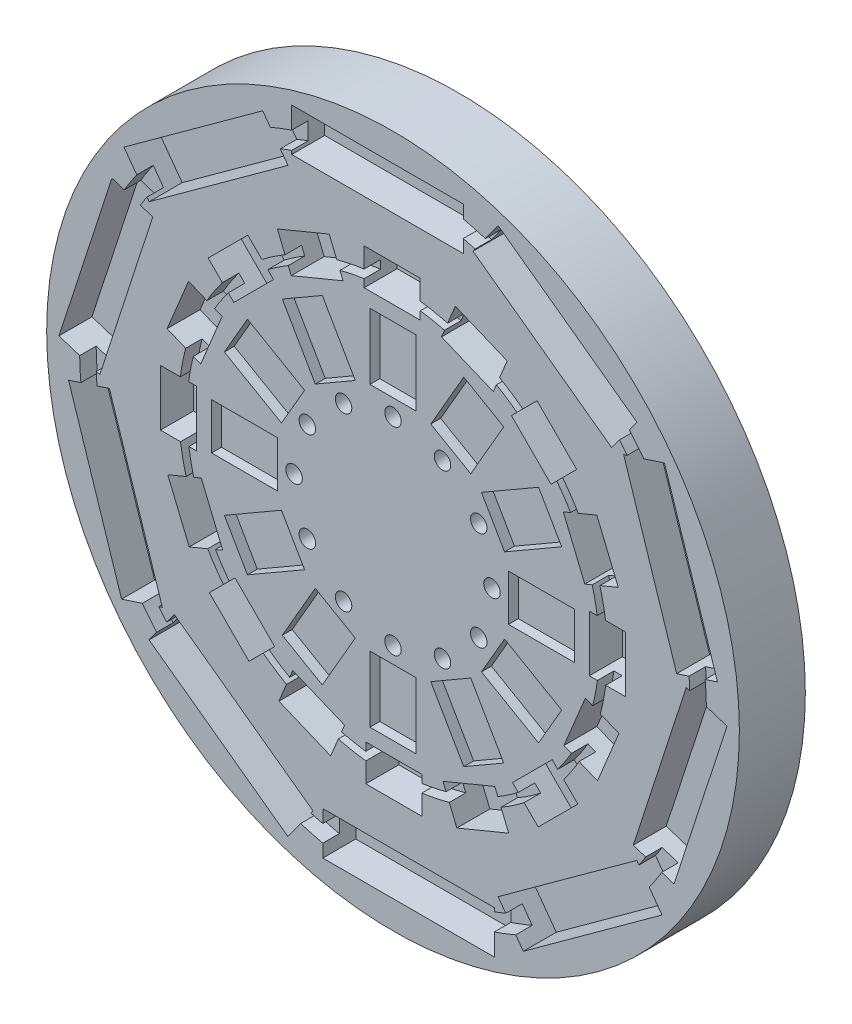
SolidWorks part; units mm, degrees
ref_plane "Front Plane" through (0, 0, 0) normal (0, 0, 1) x (1, 0, 0)
ref_plane "Top Plane" through (0, 0, 0) normal (0, 1, 0) x (1, 0, 0)
ref_plane "Right Plane" through (0, 0, 0) normal (1, 0, 0) x (0, 0, -1)
sketch "Sketch1" plane through (0, 0, 0) normal (0, 0, 1) x (1, 0, 0)
  circle A0 centre (0, 0) radius 105
  dimension "D1" = 210
extrude "Boss-Extrude1" add sketch "Sketch1" along normal blind 20
sketch "Sketch2" plane through (0, 0, 20) normal (0, 0, 1) x (1, 0, 0)
  circle A0 centre (0, 30) radius 2.5
  circle A1 centre (15, 25.9808) radius 2.5
  circle A2 centre (25.9808, 15) radius 2.5
  circle A3 centre (30, 0) radius 2.5
  circle A4 centre (25.9808, -15) radius 2.5
  circle A5 centre (15, -25.9808) radius 2.5
  circle A6 centre (0, -30) radius 2.5
  circle A7 centre (-15, -25.9808) radius 2.5
  circle A8 centre (-25.9808, -15) radius 2.5
  circle A9 centre (-30, 0) radius 2.5
  circle A10 centre (-25.9808, 15) radius 2.5
  circle A11 centre (-15, 25.9808) radius 2.5
  point P28 (0, 0)
  dimension "D2" = 5
  dimension "D1" = 30
  dimension "D3" = 12
extrude "Cut-Extrude1" cut sketch "Sketch2" against normal through all
sketch "Sketch3" plane through (0, 0, 20) normal (0, 0, 1) x (1, 0, 0)
  line L0 (23.5622, 26.8109) -> (33.5622, 44.1314)
  line L1 (7, 35) -> (-7, 35)
  line L2 (7, 35) -> (7, 55)
  line L3 (7, 55) -> (-7, 55)
  line L4 (-7, 35) -> (-7, 55)
  line L5 (7, 35) -> (-7, 55) construction
  line L6 (7, 55) -> (-7, 35) construction
  line L7 (23.5622, 26.8109) -> (11.4378, 33.8109)
  line L8 (11.4378, 33.8109) -> (21.4378, 51.1314)
  line L9 (33.5622, 44.1314) -> (21.4378, 51.1314)
  line L10 (33.8109, 11.4378) -> (51.1314, 21.4378)
  line L11 (33.8109, 11.4378) -> (26.8109, 23.5622)
  line L12 (26.8109, 23.5622) -> (44.1314, 33.5622)
  line L13 (51.1314, 21.4378) -> (44.1314, 33.5622)
  line L14 (35, -7) -> (55, -7)
  line L15 (35, -7) -> (35, 7)
  line L16 (35, 7) -> (55, 7)
  line L17 (55, -7) -> (55, 7)
  line L18 (26.8109, -23.5622) -> (44.1314, -33.5622)
  line L19 (26.8109, -23.5622) -> (33.8109, -11.4378)
  line L20 (33.8109, -11.4378) -> (51.1314, -21.4378)
  line L21 (44.1314, -33.5622) -> (51.1314, -21.4378)
  line L22 (11.4378, -33.8109) -> (21.4378, -51.1314)
  line L23 (11.4378, -33.8109) -> (23.5622, -26.8109)
  line L24 (23.5622, -26.8109) -> (33.5622, -44.1314)
  line L25 (21.4378, -51.1314) -> (33.5622, -44.1314)
  line L26 (-7, -35) -> (-7, -55)
  line L27 (-7, -35) -> (7, -35)
  line L28 (7, -35) -> (7, -55)
  line L29 (-7, -55) -> (7, -55)
  line L30 (-23.5622, -26.8109) -> (-33.5622, -44.1314)
  line L31 (-23.5622, -26.8109) -> (-11.4378, -33.8109)
  line L32 (-11.4378, -33.8109) -> (-21.4378, -51.1314)
  line L33 (-33.5622, -44.1314) -> (-21.4378, -51.1314)
  line L34 (-33.8109, -11.4378) -> (-51.1314, -21.4378)
  line L35 (-33.8109, -11.4378) -> (-26.8109, -23.5622)
  line L36 (-26.8109, -23.5622) -> (-44.1314, -33.5622)
  line L37 (-51.1314, -21.4378) -> (-44.1314, -33.5622)
  line L38 (-35, 7) -> (-55, 7)
  line L39 (-35, 7) -> (-35, -7)
  line L40 (-35, -7) -> (-55, -7)
  line L41 (-55, 7) -> (-55, -7)
  line L42 (-26.8109, 23.5622) -> (-44.1314, 33.5622)
  line L43 (-26.8109, 23.5622) -> (-33.8109, 11.4378)
  line L44 (-33.8109, 11.4378) -> (-51.1314, 21.4378)
  line L45 (-44.1314, 33.5622) -> (-51.1314, 21.4378)
  line L46 (-11.4378, 33.8109) -> (-21.4378, 51.1314)
  line L47 (-11.4378, 33.8109) -> (-23.5622, 26.8109)
  line L48 (-23.5622, 26.8109) -> (-33.5622, 44.1314)
  line L49 (-21.4378, 51.1314) -> (-33.5622, 44.1314)
  point P2 (0, 45)
  point P53 (0, 0)
  dimension "D1" = 12
  dimension "D3" = 14
  dimension "D4" = 20
extrude "Cut-Extrude6" cut sketch "Sketch3" against normal blind 3
sketch "Sketch7" plane through (0, 0, 20) normal (0, 0, 1) x (1, 0, 0)
  line L0 (30.3934, 51.813) -> (34.6029, 61.9756)
  line L1 (8.2519, 59.5) -> (-8.7481, 59.5)
  line L2 (8.2519, 59.5) -> (8.2519, 70.5)
  line L3 (8.2519, 70.5) -> (-8.7481, 70.5)
  line L4 (-8.7481, 59.5) -> (-8.7481, 70.5)
  line L5 (8.2519, 59.5) -> (-8.7481, 70.5) construction
  line L6 (8.2519, 70.5) -> (-8.7481, 59.5) construction
  line L7 (30.3934, 51.813) -> (14.6875, 58.3186)
  line L8 (14.6875, 58.3186) -> (18.897, 68.4813)
  line L9 (34.6029, 61.9756) -> (18.897, 68.4813)
  line L10 (47.9078, 36.2379) -> (55.686, 44.0161)
  line L11 (47.9078, 36.2379) -> (35.887, 48.2587)
  line L12 (35.887, 48.2587) -> (43.6652, 56.0369)
  line L13 (55.686, 44.0161) -> (43.6652, 56.0369)
  line L14 (58.1287, 15.1459) -> (68.2914, 19.3554)
  line L15 (58.1287, 15.1459) -> (51.6231, 30.8519)
  line L16 (51.6231, 30.8519) -> (61.7857, 35.0614)
  line L17 (68.2914, 19.3554) -> (61.7857, 35.0614)
  line L18 (59.5, -8.2519) -> (70.5, -8.2519)
  line L19 (59.5, -8.2519) -> (59.5, 8.7481)
  line L20 (59.5, 8.7481) -> (70.5, 8.7481)
  line L21 (70.5, -8.2519) -> (70.5, 8.7481)
  line L22 (51.813, -30.3934) -> (61.9756, -34.6029)
  line L23 (51.813, -30.3934) -> (58.3186, -14.6875)
  line L24 (58.3186, -14.6875) -> (68.4813, -18.897)
  line L25 (61.9756, -34.6029) -> (68.4813, -18.897)
  line L26 (36.2379, -47.9078) -> (44.0161, -55.686)
  line L27 (36.2379, -47.9078) -> (48.2587, -35.887)
  line L28 (48.2587, -35.887) -> (56.0369, -43.6652)
  line L29 (44.0161, -55.686) -> (56.0369, -43.6652)
  line L30 (15.1459, -58.1287) -> (19.3554, -68.2914)
  line L31 (15.1459, -58.1287) -> (30.8519, -51.6231)
  line L32 (30.8519, -51.6231) -> (35.0614, -61.7857)
  line L33 (19.3554, -68.2914) -> (35.0614, -61.7857)
  line L34 (-8.2519, -59.5) -> (-8.2519, -70.5)
  line L35 (-8.2519, -59.5) -> (8.7481, -59.5)
  line L36 (8.7481, -59.5) -> (8.7481, -70.5)
  line L37 (-8.2519, -70.5) -> (8.7481, -70.5)
  line L38 (-30.3934, -51.813) -> (-34.6029, -61.9756)
  line L39 (-30.3934, -51.813) -> (-14.6875, -58.3186)
  line L40 (-14.6875, -58.3186) -> (-18.897, -68.4813)
  line L41 (-34.6029, -61.9756) -> (-18.897, -68.4813)
  line L42 (-47.9078, -36.2379) -> (-55.686, -44.0161)
  line L43 (-47.9078, -36.2379) -> (-35.887, -48.2587)
  line L44 (-35.887, -48.2587) -> (-43.6652, -56.0369)
  line L45 (-55.686, -44.0161) -> (-43.6652, -56.0369)
  line L46 (-58.1287, -15.1459) -> (-68.2914, -19.3554)
  line L47 (-58.1287, -15.1459) -> (-51.6231, -30.8519)
  line L48 (-51.6231, -30.8519) -> (-61.7857, -35.0614)
  line L49 (-68.2914, -19.3554) -> (-61.7857, -35.0614)
  line L50 (-59.5, 8.2519) -> (-70.5, 8.2519)
  line L51 (-59.5, 8.2519) -> (-59.5, -8.7481)
  line L52 (-59.5, -8.7481) -> (-70.5, -8.7481)
  line L53 (-70.5, 8.2519) -> (-70.5, -8.7481)
  line L54 (-51.813, 30.3934) -> (-61.9756, 34.6029)
  line L55 (-51.813, 30.3934) -> (-58.3186, 14.6875)
  line L56 (-58.3186, 14.6875) -> (-68.4813, 18.897)
  line L57 (-61.9756, 34.6029) -> (-68.4813, 18.897)
  line L58 (-36.2379, 47.9078) -> (-44.0161, 55.686)
  line L59 (-36.2379, 47.9078) -> (-48.2587, 35.887)
  line L60 (-48.2587, 35.887) -> (-56.0369, 43.6652)
  line L61 (-44.0161, 55.686) -> (-56.0369, 43.6652)
  line L62 (-15.1459, 58.1287) -> (-19.3554, 68.2914)
  line L63 (-15.1459, 58.1287) -> (-30.8519, 51.6231)
  line L64 (-30.8519, 51.6231) -> (-35.0614, 61.7857)
  line L65 (-19.3554, 68.2914) -> (-35.0614, 61.7857)
  point P0 (-0.2481, 65)
  point P69 (0, 0)
  dimension "D1" = 11
  dimension "D2" = 17
  dimension "D3" = 65
  dimension "D4" = 16
extrude "Cut-Extrude8" cut sketch "Sketch7" against normal blind 10
sketch "Sketch8" plane through (0, 0, 20) normal (0, 0, 1) x (1, 0, 0)
  circle A0 centre (0, 0) radius 62.5
  circle A1 centre (0, 0) radius 65
  dimension "D1" = 125
  dimension "D2" = 130
extrude "Cut-Extrude9" cut sketch "Sketch8" against normal blind 5
sketch "Sketch9" plane through (0, 0, 20) normal (0, 0, 1) x (1, 0, 0)
  line L0 (66.3082, 55.0359) -> (73.9494, 65.5532)
  line L1 (21.2952, 83.5) -> (-30.7048, 83.5)
  line L2 (21.2952, 83.5) -> (21.2952, 96.5)
  line L3 (21.2952, 96.5) -> (-30.7048, 96.5)
  line L4 (-30.7048, 83.5) -> (-30.7048, 96.5)
  line L5 (21.2952, 83.5) -> (-30.7048, 96.5) construction
  line L6 (21.2952, 96.5) -> (-30.7048, 83.5) construction
  line L7 (66.3082, 55.0359) -> (24.2393, 85.6008)
  line L8 (24.2393, 85.6008) -> (31.8806, 96.118)
  line L9 (73.9494, 65.5532) -> (31.8806, 96.118)
  line L10 (85.9938, 5.55) -> (98.3575, 9.5672)
  line L11 (85.9938, 5.55) -> (69.9249, 55.0049)
  line L12 (69.9249, 55.0049) -> (82.2886, 59.0222)
  line L13 (98.3575, 9.5672) -> (82.2886, 59.0222)
  line L14 (72.8326, -46.0558) -> (85.1964, -50.0731)
  line L15 (72.8326, -46.0558) -> (88.9015, 3.3991)
  line L16 (88.9015, 3.3991) -> (101.2653, -0.6181)
  line L17 (85.1964, -50.0731) -> (101.2653, -0.6181)
  line L18 (31.8519, -80.0699) -> (39.4931, -90.5871)
  line L19 (31.8519, -80.0699) -> (73.9208, -49.5051)
  line L20 (73.9208, -49.5051) -> (81.562, -60.0223)
  line L21 (39.4931, -90.5871) -> (81.562, -60.0223)
  line L22 (-21.2952, -83.5) -> (-21.2952, -96.5)
  line L23 (-21.2952, -83.5) -> (30.7048, -83.5)
  line L24 (30.7048, -83.5) -> (30.7048, -96.5)
  line L25 (-21.2952, -96.5) -> (30.7048, -96.5)
  line L26 (-66.3082, -55.0359) -> (-73.9494, -65.5532)
  line L27 (-66.3082, -55.0359) -> (-24.2393, -85.6008)
  line L28 (-24.2393, -85.6008) -> (-31.8806, -96.118)
  line L29 (-73.9494, -65.5532) -> (-31.8806, -96.118)
  line L30 (-85.9938, -5.55) -> (-98.3575, -9.5672)
  line L31 (-85.9938, -5.55) -> (-69.9249, -55.0049)
  line L32 (-69.9249, -55.0049) -> (-82.2886, -59.0222)
  line L33 (-98.3575, -9.5672) -> (-82.2886, -59.0222)
  line L34 (-72.8326, 46.0558) -> (-85.1964, 50.0731)
  line L35 (-72.8326, 46.0558) -> (-88.9015, -3.3991)
  line L36 (-88.9015, -3.3991) -> (-101.2653, 0.6181)
  line L37 (-85.1964, 50.0731) -> (-101.2653, 0.6181)
  line L38 (-31.8519, 80.0699) -> (-39.4931, 90.5871)
  line L39 (-31.8519, 80.0699) -> (-73.9208, 49.5051)
  line L40 (-73.9208, 49.5051) -> (-81.562, 60.0223)
  line L41 (-39.4931, 90.5871) -> (-81.562, 60.0223)
  point P0 (-4.7048, 90)
  point P45 (0, 0)
  dimension "D1" = 13
  dimension "D2" = 52
  dimension "D3" = 90
  dimension "D4" = 10
extrude "Cut-Extrude10" cut sketch "Sketch9" against normal blind 10
sketch "Sketch10" plane through (0, 0, 20) normal (0, 0, 1) x (1, 0, 0)
  circle A0 centre (0, 0) radius 90
  circle A1 centre (0, 0) radius 95
  dimension "D1" = 180
  dimension "D2" = 190
extrude "Cut-Extrude11" cut sketch "Sketch10" against normal blind 5
